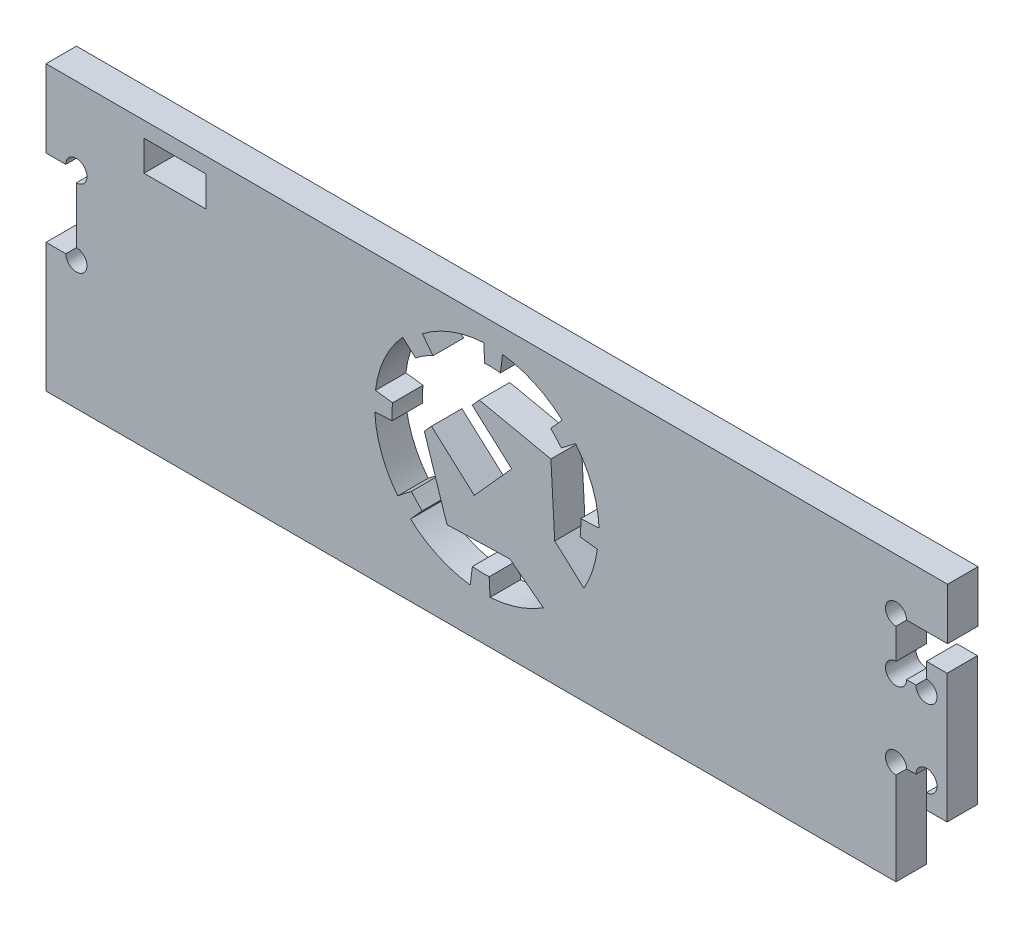
SolidWorks part; units mm, degrees
ref_plane "Front Plane" through (0, 0, 0) normal (0, 0, 1) x (1, 0, 0)
ref_plane "Top Plane" through (0, 0, 0) normal (0, 1, 0) x (1, 0, 0)
ref_plane "Right Plane" through (0, 0, 0) normal (1, 0, 0) x (0, 0, -1)
sketch "Sketch1" plane through (0, 0, 0) normal (0, 0, 1) x (1, 0, 0)
  line L1 (82.45, -27.5) -> (-82.45, -27.5)
  line L2 (82.45, -27.5) -> (82.45, 27.5)
  line L3 (82.45, 27.5) -> (-82.45, 27.5)
  line L4 (-82.45, -27.5) -> (-82.45, 27.5)
  line L5 (82.45, -27.5) -> (-82.45, 27.5) construction
  line L6 (82.45, 27.5) -> (-82.45, -27.5) construction
  point P0 (0, 0)
  dimension "D1" = 55
  dimension "D2" = 164.9
extrude "Boss-Extrude1" add sketch "Sketch1" along normal blind 5.9
sketch "Sketch2" plane through (0, 0, 5.9) normal (0, 0, 1) x (1, 0, 0)
  line L0 (-82.45, 27.5) -> (-82.45, -27.5) construction
  line L1 (-82.45, 12.5) -> (-76.55, 12.5)
  line L2 (-82.45, 12.5) -> (-82.45, -2.5)
  line L3 (-82.45, -2.5) -> (-76.55, -2.5)
  line L4 (-76.55, 12.5) -> (-76.55, -2.5)
  line L6 (-82.45, -27.5) -> (82.45, -27.5) construction
  dimension "D2" = 5.9
  dimension "D3" = 15
  dimension "D1" = 25
extrude "Cut-Extrude1" cut sketch "Sketch2" against normal through all
sketch "Sketch3" plane through (0, 0, 5.9) normal (0, 0, 1) x (1, 0, 0)
  line L0 (82.45, -7.5) -> (88.35, -7.5)
  line L1 (82.45, -27.5) -> (82.45, 27.5) construction
  line L2 (88.35, -7.5) -> (88.35, -12.5)
  line L3 (88.35, -12.5) -> (92.35, -12.5)
  line L4 (92.35, -12.5) -> (92.35, 12.5)
  line L5 (92.35, 12.5) -> (88.35, 12.5)
  line L6 (88.35, 12.5) -> (88.35, 7.5)
  line L7 (88.35, 7.5) -> (82.45, 7.5)
  line L8 (82.45, 7.5) -> (82.45, -7.5)
  line L10 (82.45, 27.5) -> (-82.45, 27.5) construction
  dimension "D1" = 15
  dimension "D2" = 25
  dimension "D3" = 4
  dimension "D4" = 5.9
  dimension "D5" = 20
extrude "Boss-Extrude2" add sketch "Sketch3" against normal up to surface (5.9 mm away) up to face at (-39.75, 2.5, 0)
sketch "Sketch4" plane through (0, 0, 5.9) normal (0, 0, 1) x (1, 0, 0)
  line L298 (-23.4574, 13.0173) -> (-82.0874, 13.0173) construction
  line L595 (29.1083, 13.0173) -> (87.7382, 13.0173) construction
  line L596 (3.5158, -15.7062) -> (3.6928, -19.0808)
  line L597 (-0.1565, -18.9403) -> (0.2714, -15.6026)
  line L598 (-9.4954, -11.1528) -> (-11.7426, -13.6419)
  line L599 (-14.2217, -10.9811) -> (-11.5742, -8.9173)
  line L600 (-15.3101, 1.0833) -> (-18.6637, 0.9074)
  line L601 (-18.542, 4.5649) -> (-15.2033, 4.1605)
  line L602 (-10.7642, 13.8973) -> (-13.2552, 16.1469)
  line L603 (-7.3661, 15.9794) -> (-9.4432, 18.6359)
  line L604 (6.1043, 22.9569) -> (5.7028, 19.6212)
  line L605 (2.6459, 19.7315) -> (2.4746, 23.1052)
  line L606 (15.4451, 15.1867) -> (17.6921, 17.6802)
  line L607 (20.2695, 15.0345) -> (17.535, 12.9415)
  line L608 (21.2859, 2.9419) -> (24.8373, 3.1282)
  line L609 (24.5075, -0.5946) -> (21.1718, -0.1806)
  line L610 (16.2377, -3.3374) -> (21.8959, -8.4512)
  line L611 (15.4954, 10.0651) -> (16.2377, -3.3374)
  line L612 (1.6031, 13.0173) -> (15.4954, 10.0651)
  line L613 (0.2197, 11.481) -> (1.6031, 13.0173)
  line L614 (7.8891, 4.5894) -> (0.2197, 11.481)
  line L615 (0.6383, -3.4802) -> (7.8891, 4.5894)
  line L616 (7.5252, -10.708) -> (14.033, -15.6686)
  line L617 (-4.6673, -11.0417) -> (7.5252, -10.708)
  line L618 (-9.0563, 2.4657) -> (-4.6673, -11.0417)
  line L619 (-7.6725, 3.9875) -> (-9.0563, 2.4657)
  line L620 (0.6383, -3.4802) -> (-7.6725, 3.9875)
  arc A152 (0.2714, -15.6026) -> (3.5158, -15.7062) centre (2.544, 4.6992) ccw
  arc A153 (-11.5742, -8.9173) -> (-9.4954, -11.1528) centre (31.7956, 29.3269) ccw
  arc A154 (-15.2033, 4.1605) -> (-15.3101, 1.0833) centre (-0.7127, 2.1172) ccw
  arc A155 (-7.3661, 15.9794) -> (-10.7642, 13.8973) centre (-1.6678, 2.8652) ccw
  arc A156 (5.7028, 19.6212) -> (2.6459, 19.7315) centre (3.5975, 3.6961) ccw
  arc A157 (17.535, 12.9415) -> (15.4451, 15.1867) centre (-17.1744, -17.2714) ccw
  arc A158 (21.1718, -0.1806) -> (21.2859, 2.9419) centre (0.1233, 2.152) ccw
  arc A159 (3.6928, -19.0808) -> (14.033, -15.6686) centre (2.2933, 2.5338) ccw
  arc A160 (-11.7426, -13.6419) -> (-0.1565, -18.9403) centre (2.455, 2.087) ccw
  arc A161 (-18.6637, 0.9074) -> (-14.2217, -10.9811) centre (2.1027, 1.8926) ccw
  arc A162 (-13.2552, 16.1469) -> (-18.542, 4.5649) centre (2.1548, 2.1151) ccw
  arc A163 (-9.4432, 18.6359) -> (2.4746, 23.1052) centre (3.796, 1.4567) cw
  arc A164 (17.6921, 17.6802) -> (6.1043, 22.9569) centre (3.5364, 1.9563) ccw
  arc A165 (24.8373, 3.1282) -> (20.2695, 15.0345) centre (5.0239, 2.3563) ccw
  arc A166 (21.8959, -8.4512) -> (24.5075, -0.5946) centre (2.9697, 2.2024) ccw
  point P719 (-9.0563, 2.4657)
  point P720 (-4.6673, -11.0417)
  point P721 (7.5252, -10.708)
  point P722 (14.033, -15.6686)
  point P723 (3.6928, -19.0808)
  point P724 (3.5158, -15.7062)
  point P725 (0.2714, -15.6026)
  point P726 (-0.1565, -18.9403)
  point P727 (-11.7426, -13.6419)
  point P728 (-9.4954, -11.1528)
  point P729 (-11.5742, -8.9173)
  point P730 (-14.2217, -10.9811)
  point P731 (-18.6637, 0.9074)
  point P732 (-15.3101, 1.0833)
  point P733 (-15.2033, 4.1605)
  point P734 (-18.542, 4.5649)
  point P735 (-13.2552, 16.1469)
  point P736 (-10.7642, 13.8973)
  point P737 (-7.3661, 15.9794)
  point P738 (-9.4432, 18.6359)
  point P739 (2.4746, 23.1052)
  point P740 (2.6459, 19.7315)
  point P741 (6.1043, 22.9569)
  point P742 (5.7028, 19.6212)
  point P743 (17.535, 12.9415)
  point P744 (15.4451, 15.1867)
  point P745 (17.6921, 17.6802)
  point P746 (20.2695, 15.0345)
  point P747 (24.8373, 3.1282)
  point P748 (21.2859, 2.9419)
  point P749 (21.1718, -0.1806)
  point P750 (16.2377, -3.3374)
  point P751 (15.4954, 10.0651)
  point P752 (1.6031, 13.0173)
  point P753 (0.2197, 11.481)
  point P754 (7.8891, 4.5894)
  point P755 (24.5075, -0.5946)
  point P756 (21.8959, -8.4512)
  point P757 (0.6383, -3.4802)
  point P758 (-7.6725, 3.9875)
extrude "Cut-Extrude2" cut sketch "Sketch4" against normal blind 10
sketch "Sketch5" plane through (0, 0, 0) normal (0, 0, -1) x (-1, 0, 0)
  line L1 (-82.45, 27.5) -> (-92.45, 27.5)
  line L2 (-82.45, 27.5) -> (-82.45, 17.5)
  line L3 (-82.45, 17.5) -> (-92.45, 17.5)
  line L4 (-92.45, 27.5) -> (-92.45, 17.5)
  line L5 (-82.45, 27.5) -> (-92.45, 17.5) construction
  line L6 (-82.45, 17.5) -> (-92.45, 27.5) construction
  point P4 (-87.45, 22.5)
  dimension "D1" = 10
  dimension "D2" = 10
extrude "Boss-Extrude3" add sketch "Sketch5" against normal up to surface (5.9 mm away) up to face at (2.3718, 2.6627, 5.9)
sketch "Sketch6" plane through (0, 0, 0) normal (0, 0, -1) x (-1, 0, 0)
  circle A0 centre (-82.45, -7.5) radius 2.05
  circle A1 centre (-88.35, -7.5) radius 2.05
  circle A2 centre (-88.35, 7.5) radius 2.05
  circle A3 centre (-82.45, 7.5) radius 2.05
  circle A4 centre (-82.45, 17.5) radius 2.05
  circle A5 centre (76.55, 12.5) radius 2.05
  circle A6 centre (76.55, -2.5) radius 2.05
  dimension "D1" = 4.1
extrude "Cut-Extrude3" cut sketch "Sketch6" against normal up to next
sketch "Sketch7" plane through (0, 0, 0) normal (0, 0, -1) x (-1, 0, 0)
  line L0 (51.45, 24.5) -> (63.45, 24.5)
  line L1 (51.45, 24.5) -> (51.45, 18.6)
  line L2 (51.45, 18.6) -> (63.45, 18.6)
  line L3 (63.45, 24.5) -> (63.45, 18.6)
  line L4 (51.45, 24.5) -> (63.45, 18.6) construction
  line L5 (51.45, 18.6) -> (63.45, 24.5) construction
  line L6 (-92.45, 27.5) -> (82.45, 27.5) construction
  line L9 (82.45, 27.5) -> (82.45, 12.5) construction
  point P4 (57.45, 21.55)
  dimension "D2" = 5.9
  dimension "D1" = 12
  dimension "D3" = 3
  dimension "D4" = 25
extrude "Cut-Extrude4" cut sketch "Sketch7" against normal up to next
equation "\"e\" = 5.9"
equation "\"D1@Boss-Extrude1\"= \"e\""
equation "\"D2@Sketch2\"= \"e\""
equation "\"D4@Sketch3\"= \"e\""
equation "\"D2@Sketch7\"= \"e\""
equation "\"D2@Sketch1\"= 159 + \"e\""
